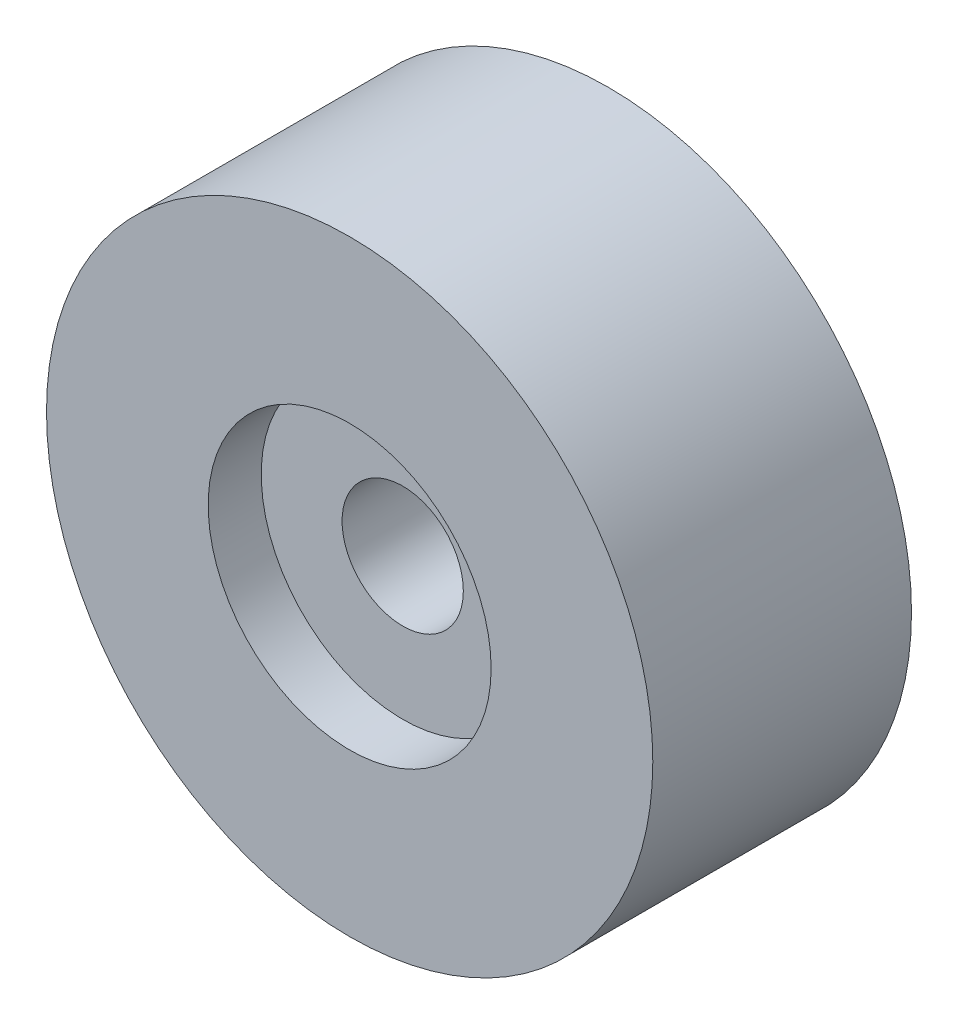
SolidWorks part; units mm, degrees
ref_plane "正面" through (0, 0, 0) normal (0, 0, 1) x (1, 0, 0)
ref_plane "平面" through (0, 0, 0) normal (0, 1, 0) x (1, 0, 0)
ref_plane "右側面" through (0, 0, 0) normal (1, 0, 0) x (0, 0, -1)
sketch "ｽｹｯﾁ1" plane through (0, 0, 0) normal (0, 0, 1) x (1, 0, 0)
  circle A8 centre (0, 0) radius 30
  circle A9 centre (0, 0) radius 6
extrude "ﾎﾞｽ - 押し出し1" add sketch "ｽｹｯﾁ1" along normal blind 25.6
sketch "ｽｹｯﾁ2" plane through (0, 0, 25.6) normal (0, 0, 1) x (1, 0, 0)
  circle A0 centre (0, 0) radius 14
extrude "ｶｯﾄ - 押し出し1" cut sketch "ｽｹｯﾁ2" against normal blind 5.25
